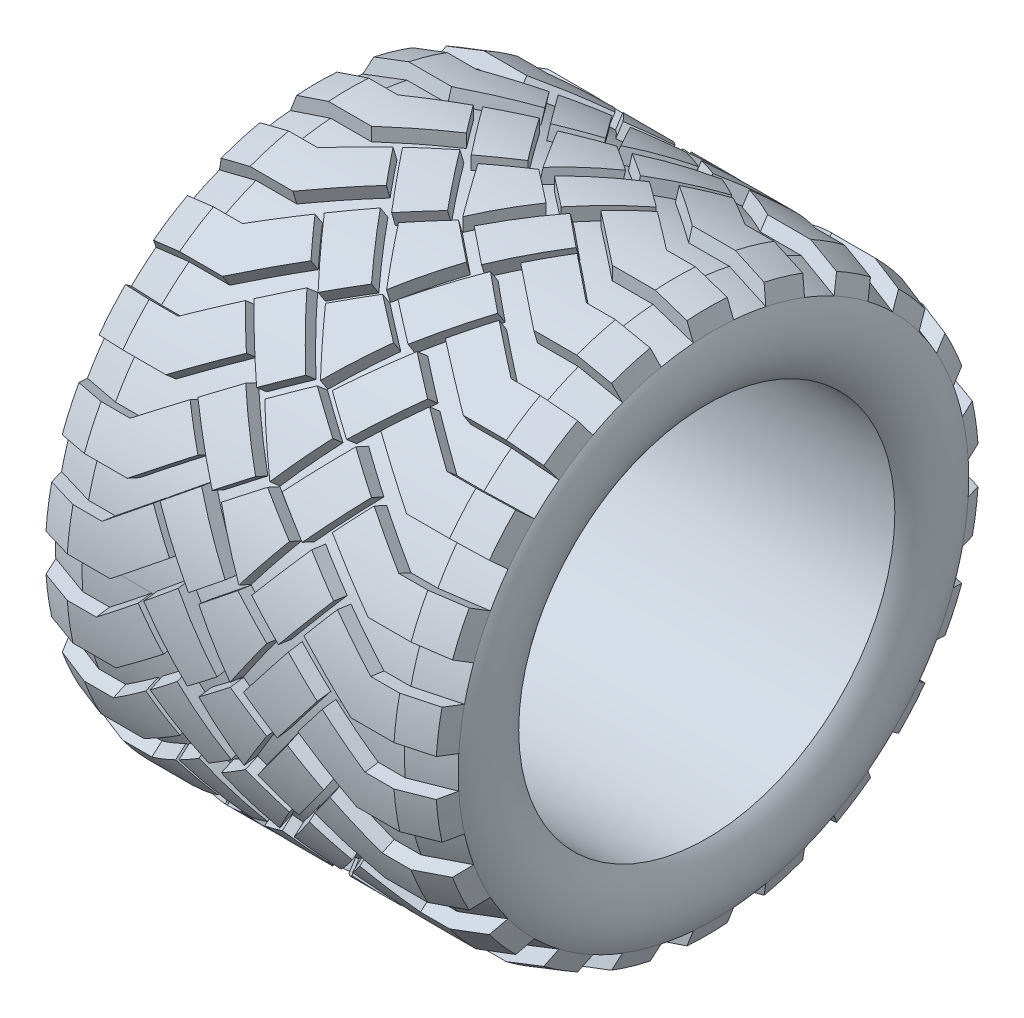
SolidWorks part; units mm, degrees
ref_plane "Front Plane" through (0, 0, 0) normal (0, 0, 1) x (1, 0, 0)
ref_plane "Top Plane" through (0, 0, 0) normal (0, 1, 0) x (1, 0, 0)
ref_plane "Right Plane" through (0, 0, 0) normal (1, 0, 0) x (0, 0, -1)
sketch "Sketch1" plane through (0, 0, 0) normal (0, 1, 0) x (1, 0, 0)
  line L0 (-25, 0) -> (25, 0) construction
  line L1 (0, 35.0731) -> (0, -36.303) construction
  line L2 (-12, 20) -> (12, 20)
  line L3 (-14.5, 14) -> (14.5, 14)
  line L5 (-15, 19) -> (-12, 20)
  line L6 (15, 19) -> (12, 20)
  arc A0 (-15, 19) -> (-14.5, 14) centre (-11.115, 16.8635) ccw
  arc A1 (15, 19) -> (14.5, 14) centre (11.115, 16.8635) cw
  dimension "D1" = 50
  dimension "D2" = 25
  dimension "D3" = 29
  dimension "D5" = 40
  dimension "D6" = 28
  dimension "D12" = 3
revolve "Revolve1" add sketch "Sketch1" angle 360 about L0
ref_plane "Plane1" through (0, 20, 0) normal (0, 1, 0) x (1, 0, 0)
sketch "Sketch2" plane through (0, 20, 0) normal (0, 1, 0) x (1, 0, 0)
  line L0 (-15, 0) -> (15, 0) construction
  line L1 (-15, -19) -> (-15, 19) construction
  line L2 (15, -19) -> (15, 19) construction
  line L3 (0, 20) -> (0, -20) construction
  line L4 (12, 20) -> (-12, 20) construction
  line L5 (-12, -20) -> (12, -20) construction
  line L6 (-15, 1.5) -> (-15, -1.5)
  line L7 (-15, 1.5) -> (-10, 1.5)
  line L8 (-10, 1.5) -> (-6.8534, 3.9696)
  line L9 (-6.8534, 3.9696) -> (-5.0012, 1.6096)
  line L10 (-5.0012, 1.6096) -> (-8.9633, -1.5)
  line L11 (-8.9633, -1.5) -> (-15, -1.5)
  line L12 (-12, -20) -> (-12, 20) construction
  line L13 (5.0012, 1.6096) -> (8.9633, -1.5)
  line L14 (6.8534, 3.9696) -> (5.0012, 1.6096)
  line L15 (10, 1.5) -> (6.8534, 3.9696)
  line L16 (15, 1.5) -> (10, 1.5)
  line L17 (15, 1.5) -> (15, -1.5)
  line L18 (8.9633, -1.5) -> (15, -1.5)
  line L19 (-6.4601, 4.2783) -> (-3.3485, 0.3136)
  line L20 (-3.3485, 0.3136) -> (-0.9885, 2.1658)
  line L21 (-0.9885, 2.1658) -> (-4.1001, 6.1305)
  line L22 (-4.1001, 6.1305) -> (-6.4601, 4.2783)
  line L23 (0.9885, 2.1658) -> (4.1001, 6.1305)
  line L24 (3.3485, 0.3136) -> (0.9885, 2.1658)
  line L25 (6.4601, 4.2783) -> (3.3485, 0.3136)
  line L26 (4.1001, 6.1305) -> (6.4601, 4.2783)
  line L27 (-2.5333, 0) -> (0, 1.9882)
  line L28 (0, 1.9882) -> (2.5333, 0)
  line L29 (2.5333, 0) -> (0, -3.6607)
  line L30 (0, -3.6607) -> (-2.5333, 0)
  dimension "D1" = 1.5
  dimension "D2" = 3
  dimension "D3" = 2
  dimension "D4" = 3
  dimension "D5" = 4
  dimension "D6" = 0.5
  dimension "D7" = 3
  dimension "D8" = 0.75
  dimension "D9" = 0.75
extrude "Boss-Extrude1" add sketch "Sketch2" along normal mid plane 5
sketch "Sketch4" plane through (0, 0, 0) normal (0, 1, 0) x (1, 0, 0)
  line L12 (-15.3162, 19.9487) -> (-15.3162, 32.8969)
  line L13 (-15.3162, 32.8969) -> (15.3162, 32.8969)
  line L14 (15.3162, 32.8969) -> (15.3162, 19.9487)
  line L15 (15.3162, 19.9487) -> (12.1623, 21)
  line L16 (12.1623, 21) -> (-12.1623, 21)
  line L17 (-12.1623, 21) -> (-15.3162, 19.9487)
  line L18 (14.5265, 20.2119) -> (12.1623, 21)
  line L19 (12.1623, 21) -> (-12.1623, 21)
  line L20 (-12.1623, 21) -> (-14.5265, 20.2119)
  line L21 (-15, 0) -> (15, 0) construction
  line L22 (-15, 1.5) -> (-15, -1.5) construction
  line L23 (15, -1.5) -> (15, 1.5) construction
  line L24 (-15, 19) -> (-14.5265, 20.2119)
  line L25 (0, 20) -> (0, -20) construction
  line L26 (12, 20) -> (-12, 20) construction
  line L27 (-12, -20) -> (12, -20) construction
  line L28 (15, 19) -> (14.5265, 20.2119)
  line L29 (-15, 19) -> (-15.3162, 19.9487)
  line L30 (15, 19) -> (15.3162, 19.9487)
  dimension "D1" = 1
pattern_circular "CirPattern1" count 22 over 360 about axis through (0, 0, 0) along (1, 0, 0) of "Boss-Extrude1"
revolve "Cut-Revolve1" cut sketch "Sketch4" angle 360 about L21
